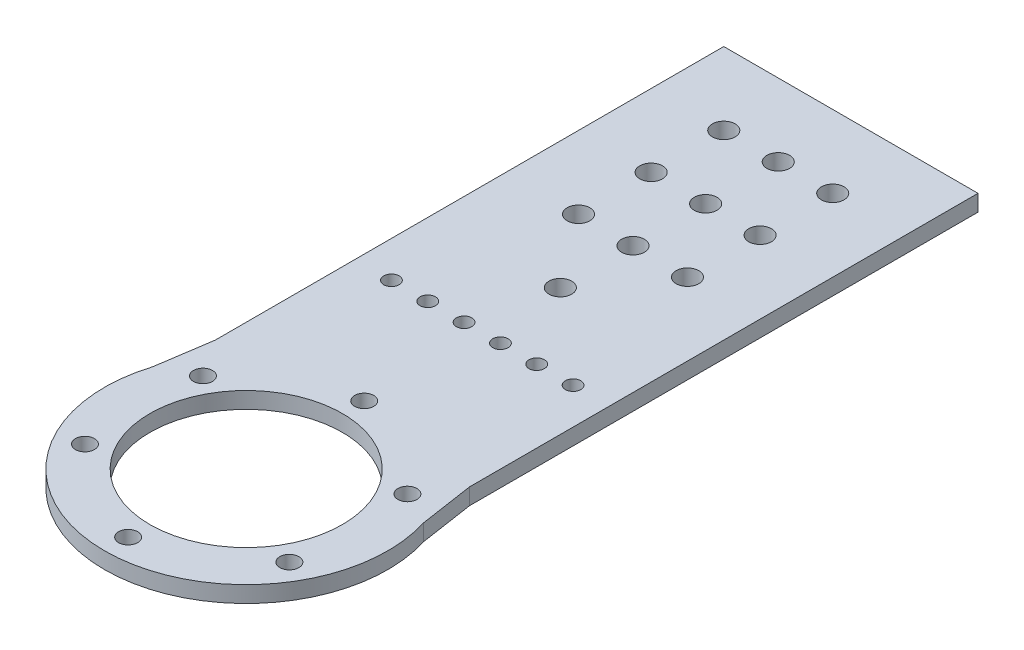
SolidWorks part; units mm, degrees
ref_plane "Front Plane" through (0, 0, 0) normal (0, 0, 1) x (1, 0, 0)
ref_plane "Top Plane" through (0, 0, 0) normal (0, 1, 0) x (1, 0, 0)
ref_plane "Right Plane" through (0, 0, 0) normal (1, 0, 0) x (0, 0, -1)
sketch "Sketch1" plane through (0, 0, 0) normal (0, 1, 0) x (1, 0, 0)
  circle A0 centre (0, 0) radius 45 construction
  circle A1 centre (0, 0) radius 39
  circle A2 centre (0, 0) radius 26.5
  circle A3 centre (0, 0) radius 32.5 construction
  dimension "D1" = 90
  dimension "D2" = 65
  dimension "D3" = 78
  dimension "D4" = 53
extrude "Boss-Extrude1" add sketch "Sketch1" along normal mid plane 4.5
sketch "Sketch3" plane through (0, 0, 0) normal (0, 1, 0) x (1, 0, 0)
  line L0 (0, 0) -> (0, 78) construction
  line L2 (-25, 78) -> (25, 78)
  line L3 (-25, 78) -> (-25, 26.5)
  line L4 (-25, 26.5) -> (25, 26.5)
  line L5 (25, 78) -> (25, 26.5)
  line L6 (0, 26.5) -> (0, 78) construction
  line L7 (-25, 52.25) -> (25, 52.25) construction
  circle A0 centre (0, 0) radius 26.5 construction
  point P3 (0, 52.25)
  dimension "D1" = 78
  dimension "D2" = 50
extrude "Boss-Extrude2" add sketch "Sketch3" along normal mid plane 4.5
sketch "Sketch4" plane through (0, 0, 0) normal (0, 1, 0) x (1, 0, 0)
  line L0 (-25, 53.9666) -> (-37.4668, 10.8276)
  line L1 (-25, 78) -> (-25, 29.9333) construction
  line L2 (-37.4668, 10.8276) -> (-25, 29.9333)
  line L3 (-25, 29.9333) -> (-25, 53.9666)
  line L4 (0, 0) -> (0, 78) construction
  line L5 (25, 78) -> (-25, 78) construction
  line L6 (37.4668, 10.8276) -> (25, 29.9333)
  line L7 (25, 53.9666) -> (37.4668, 10.8276)
  line L8 (25, 29.9333) -> (25, 53.9666)
  circle A0 centre (0, 0) radius 39 construction
extrude "Boss-Extrude3" [suppressed] add sketch "Sketch4" along normal mid plane 4.5
sketch "Sketch6" plane through (0, 0, 0) normal (0, 1, 0) x (1, 0, 0)
  line L0 (0, 0) -> (0, 96.5) construction
  line L1 (-35, 166.5) -> (-35, 26.5)
  line L2 (-35, 166.5) -> (35, 166.5)
  line L4 (35, 166.5) -> (35, 26.5)
  line L5 (0, 26.5) -> (0, 166.5) construction
  line L6 (-35, 96.5) -> (35, 96.5) construction
  line L7 (-35, 26.5) -> (-39, 0)
  line L8 (35, 26.5) -> (39, 0)
  line L9 (39, 0) -> (16.5208, 26.5)
  line L10 (16.5208, 26.5) -> (-14.9815, 26.5)
  line L11 (-14.9815, 26.5) -> (-39, 0)
  circle A0 centre (0, 0) radius 26.5 construction
  circle A1 centre (0, 0) radius 39 construction
  dimension "D1" = 70
  dimension "D2" = 140
extrude "Boss-Extrude4" add sketch "Sketch6" along normal mid plane 4.5
sketch "Sketch2" plane through (0, 0, 0) normal (0, 1, 0) x (1, 0, 0)
  circle A0 centre (0, 0) radius 32.5 construction
  circle A1 centre (0, 32.5) radius 2.625
  dimension "D1" = 65
  dimension "D2" = 5.25
extrude "Cut-Extrude1" cut sketch "Sketch2" against normal through all both and the other way through all contours A1
pattern_circular "CirPattern1" count 6 over 360 about axis through (0, 0, 0) along (0, 1, 0) of "Cut-Extrude1"
sketch "Sketch7" plane through (0, 2.25, 0) normal (0, 1, 0) x (1, 0, 0)
  line L0 (0, 0) -> (0, 166.5) construction
  line L1 (35, 166.5) -> (-35, 166.5) construction
  line L2 (-15, 146.5) -> (15, 146.5) construction
  circle A0 centre (-15, 146.5) radius 3.125
  circle A1 centre (15, 146.5) radius 3.125
  point P8 (0, 146.5)
  dimension "D1" = 6.25
  dimension "D2" = 20
  dimension "D3" = 30
extrude "Cut-Extrude3" cut sketch "Sketch7" against normal through all both and the other way through all
pattern_linear "LPattern3" count 3 spacing 20 along (0, 0, 1) of "Cut-Extrude3"
sketch "Sketch8" plane through (0, 2.25, 0) normal (0, 1, 0) x (1, 0, 0)
  line L0 (0, 0) -> (0, 166.5) construction
  line L1 (35, 166.5) -> (-35, 166.5) construction
  circle A0 centre (0, 146.5) radius 3.125
  dimension "D1" = 6.25
  dimension "D2" = 20
extrude "Cut-Extrude4" cut sketch "Sketch8" against normal blind 10
pattern_linear "LPattern4" count 4 spacing 20 along (0, 0, 1) of "Cut-Extrude4"
sketch "Sketch9" plane through (0, 2.25, 0) normal (0, 1, 0) x (1, 0, 0)
  line L0 (-35, 65) -> (35, 65) construction
  line L1 (-35, 166.5) -> (-35, 26.5) construction
  line L2 (35, 26.5) -> (35, 166.5) construction
  circle A0 centre (25, 65) radius 2.125
  circle A1 centre (0, 0) radius 26.5 construction
  dimension "D1" = 4.25
  dimension "D3" = 10
  dimension "D2" = 65
extrude "Cut-Extrude5" cut sketch "Sketch9" against normal through all both and the other way through all
pattern_linear "LPattern5" count 3 spacing 10 along (-1, 0, 0) of "Cut-Extrude5"
mirror "Mirror1" about plane through (0, 0, 0) normal (1, 0, 0) of "LPattern5", "Cut-Extrude5"
